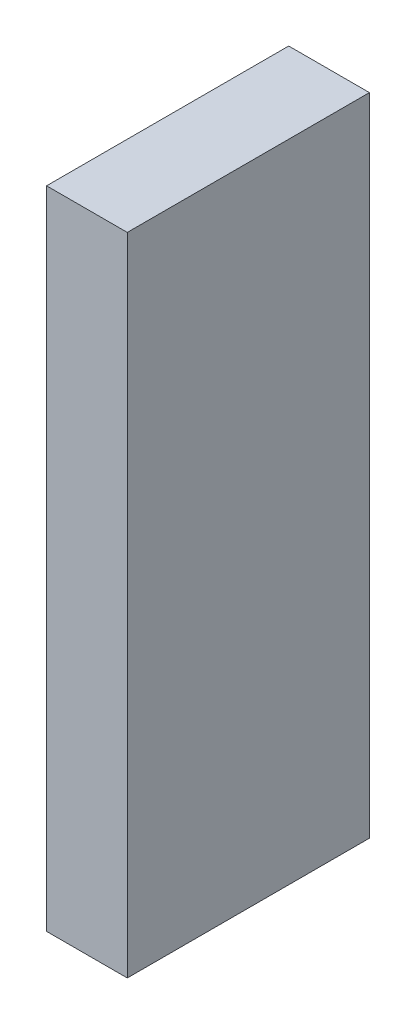
SolidWorks part; units mm, degrees
material "POLYURETHANE (11671)"
ref_plane "Front Plane" through (0, 0, 0) normal (0, 0, 1) x (1, 0, 0)
ref_plane "Top Plane" through (0, 0, 0) normal (0, 1, 0) x (1, 0, 0)
ref_plane "Right Plane" through (0, 0, 0) normal (1, 0, 0) x (0, 0, -1)
sketch "Sketch1" plane through (0, 0, 0) normal (1, 0, 0) x (0, 0, -1)
  line L1 (-4.7625, -12.7) -> (4.7625, -12.7)
  line L2 (-4.7625, -12.7) -> (-4.7625, 12.7)
  line L3 (-4.7625, 12.7) -> (4.7625, 12.7)
  line L4 (4.7625, -12.7) -> (4.7625, 12.7)
  line L5 (-4.7625, -12.7) -> (4.7625, 12.7) construction
  line L6 (-4.7625, 12.7) -> (4.7625, -12.7) construction
  point P0 (0, 0)
  dimension "D1" = 9.525
  dimension "D2" = 25.4
extrude "Boss-Extrude1" add sketch "Sketch1" along normal blind 3.175
